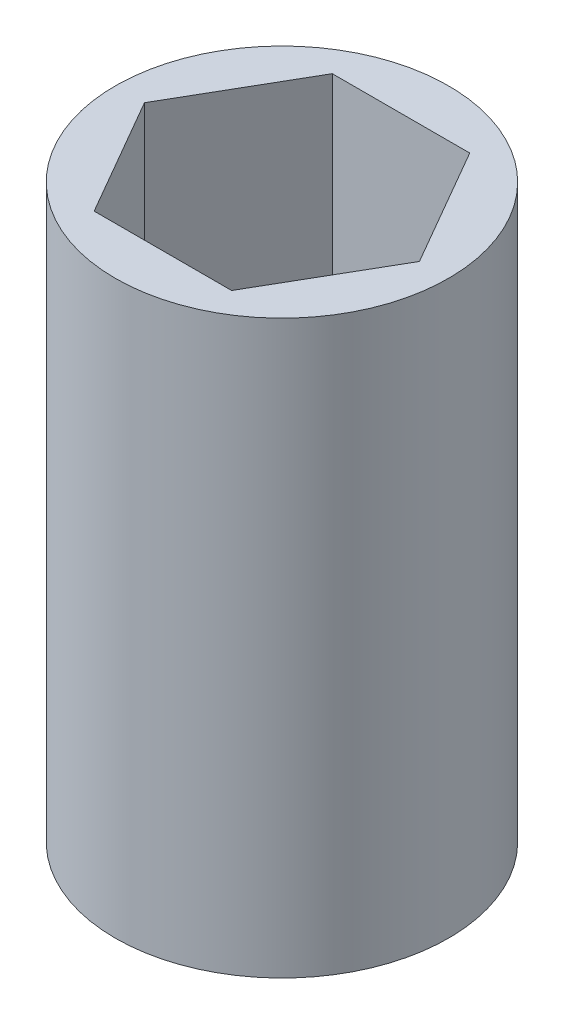
SolidWorks part; units mm, degrees
ref_plane "Front Plane" through (0, 0, 0) normal (0, 0, 1) x (1, 0, 0)
ref_plane "Top Plane" through (0, 0, 0) normal (0, 1, 0) x (1, 0, 0)
ref_plane "Right Plane" through (0, 0, 0) normal (1, 0, 0) x (0, 0, -1)
sketch "Sketch1" plane through (0, 0, 0) normal (0, 1, 0) x (1, 0, 0)
  circle A0 centre (0, 0) radius 3.5
extrude "Boss-Extrude1" add sketch "Sketch1" along normal blind 12
sketch "Sketch2" plane through (0, 12, 0) normal (0, 1, 0) x (1, 0, 0)
  line L1 (2.8868, 0) -> (1.4434, 2.5)
  line L2 (1.4434, 2.5) -> (-1.4434, 2.5)
  line L3 (-1.4434, 2.5) -> (-2.8868, 0)
  line L4 (-2.8868, 0) -> (-1.4434, -2.5)
  line L5 (-1.4434, -2.5) -> (1.4434, -2.5)
  line L6 (1.4434, -2.5) -> (2.8868, 0)
  circle A0 centre (0, 0) radius 2.5 construction
extrude "Cut-Extrude1" cut sketch "Sketch2" against normal blind 10
